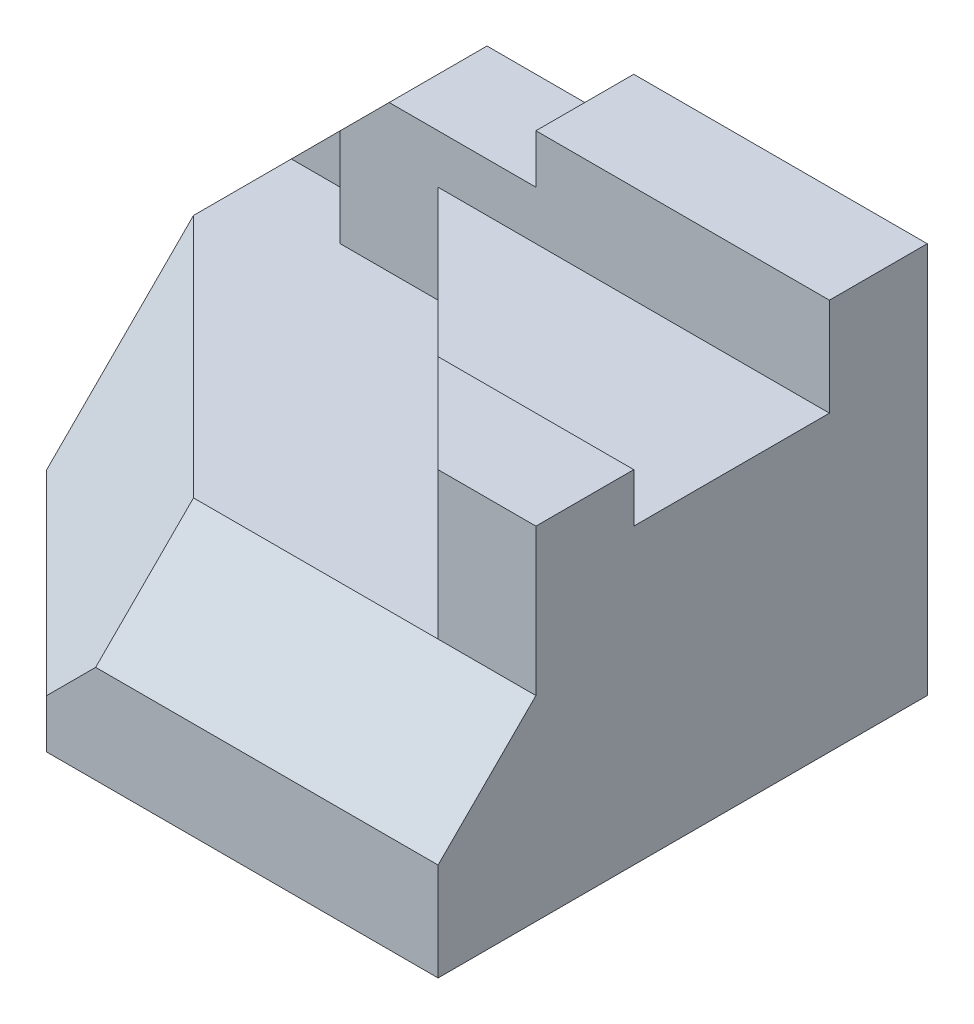
SolidWorks part; units mm, degrees
ref_plane "Front Plane" through (0, 0, 0) normal (0, 0, 1) x (1, 0, 0)
ref_plane "Top Plane" through (0, 0, 0) normal (0, 1, 0) x (1, 0, 0)
ref_plane "Right Plane" through (0, 0, 0) normal (1, 0, 0) x (0, 0, -1)
sketch "Sketch1" plane through (0, 0, 0) normal (0, 0, 1) x (1, 0, 0)
  line L1 (0, 0) -> (120, 0)
  line L2 (0, 0) -> (0, 80)
  line L3 (0, 80) -> (120, 80)
  line L4 (120, 0) -> (120, 80)
  dimension "D1" = 120
  dimension "D2" = 80
extrude "Boss-Extrude1" add sketch "Sketch1" along normal blind 100
sketch "Sketch2" plane through (0, 80, 0) normal (0, 1, 0) x (1, 0, 0)
  line L0 (0, -60) -> (40, -100)
  line L1 (0, -100) -> (0, 0) construction
  line L2 (120, -100) -> (0, -100) construction
  line L3 (40, -100) -> (0, -100)
  line L4 (0, -100) -> (0, -60)
  dimension "D1" = 40
  dimension "D2" = 40
extrude "Cut-Extrude1" cut sketch "Sketch2" against normal blind 100
sketch "Sketch3" plane through (0, 0, 0) normal (0, 0, -1) x (-1, 0, 0)
  line L0 (0, 40) -> (-30, 70)
  line L1 (0, 80) -> (0, 0) construction
  line L2 (-30, 70) -> (-60, 70)
  line L3 (-60, 70) -> (-60, 80)
  line L4 (-120, 80) -> (0, 80) construction
  line L5 (-60, 80) -> (0, 80)
  line L6 (0, 80) -> (0, 40)
  dimension "D1" = 60
  dimension "D2" = 40
  dimension "D3" = 30
  dimension "D4" = 30
extrude "Cut-Extrude2" cut sketch "Sketch3" against normal blind 100
ref_plane "Plane1" through (0, 40, 0) normal (0, 1, 0) x (1, 0, 0)
sketch "Sketch4" plane through (0, 40, 0) normal (0, 1, 0) x (1, 0, 0)
  line L0 (0, -60) -> (0, 0) construction
  line L1 (0, -20) -> (120, -20)
  line L2 (0, -20) -> (0, -100)
  line L3 (0, -100) -> (120, -100)
  line L4 (120, -20) -> (120, -100)
  dimension "D1" = 20
  dimension "D2" = 0
  dimension "D3" = 0
extrude "Cut-Extrude3" cut sketch "Sketch4" along normal blind 100
sketch "Sketch5" plane through (0, 0, 20) normal (0, 0, 1) x (1, 0, 0)
  line L0 (20, 40) -> (20, 60)
  line L1 (120, 40) -> (0, 40) construction
  line L2 (30, 70) -> (0, 40) construction
  line L3 (20, 60) -> (0, 40)
  line L4 (0, 40) -> (20, 40)
  dimension "D1" = 20
extrude "Cut-Extrude4" cut sketch "Sketch5" against normal blind 10
sketch "Sketch6" plane through (0, 40, 0) normal (0, 1, 0) x (1, 0, 0)
  line L0 (40, -20) -> (120, -20)
  line L1 (120, -20) -> (20, -20) construction
  line L2 (120, -20) -> (120, -80)
  line L3 (120, -100) -> (120, -20) construction
  line L4 (120, -80) -> (100, -80)
  line L5 (100, -80) -> (40, -20)
  dimension "D1" = 20
  dimension "D2" = 60
  dimension "D3" = 20
extrude "Boss-Extrude4" add sketch "Sketch6" along normal blind 20
sketch "Sketch8" plane through (0, 60, 0) normal (0, 1, 0) x (1, 0, 0)
  line L0 (80, -60) -> (120, -60)
  line L1 (40, -20) -> (100, -80) construction
  line L2 (120, -80) -> (120, -20) construction
  line L3 (120, -60) -> (120, -80)
  line L4 (120, -80) -> (100, -80)
  line L5 (100, -80) -> (80, -60)
  dimension "D1" = 20
extrude "Boss-Extrude5" add sketch "Sketch8" along normal blind 10
sketch "Sketch9" plane through (120, 0, 0) normal (1, 0, 0) x (0, 0, -1)
  line L0 (-100, 20) -> (-80, 40)
  line L1 (-100, 0) -> (-100, 40) construction
  line L2 (-80, 70) -> (-80, 40) construction
  line L3 (-80, 40) -> (-80, 20)
  line L4 (-80, 20) -> (-100, 20)
  line L5 (-100, 20) -> (-100, 40)
  line L6 (-100, 40) -> (-80, 40)
  dimension "D1" = 20
  dimension "D2" = 20
extrude "Cut-Extrude8" cut sketch "Sketch9" against normal blind 156 contours L6 L0 L5
sketch "Sketch10" plane through (0, 40, 0) normal (0, 1, 0) x (1, 0, 0)
  line L0 (0, -30) -> (50, -80)
  line L1 (0, -60) -> (0, -10) construction
  line L2 (20, -80) -> (100, -80) construction
  dimension "D1" = 30
  dimension "D2" = 10
sketch "Sketch12" plane through (-30, 0, 30) normal (-0.7071, 0, 0.7071) x (0.7071, 0, 0.7071)
  line L0 (42.4264, 10) -> (98.9949, 10)
  line L1 (42.4264, 0) -> (42.4264, 40) construction
  line L2 (98.9949, 20) -> (98.9949, 0) construction
  dimension "D1" = 10
ref_plane "Plane3" through (-23.3333, 23.3333, 23.3333) normal (-0.5774, 0.5774, 0.5774) x (0.8165, 0.4082, 0.4082)
sketch "Sketch13" plane through (-23.3333, 23.3333, 23.3333) normal (-0.5774, 0.5774, 0.5774) x (0.8165, 0.4082, 0.4082)
  line L0 (28.5774, 7.0711) -> (28.5774, -35.3553)
  line L1 (28.5774, -35.3553) -> (77.5672, -63.6396)
  line L2 (77.5672, -63.6396) -> (89.8146, -28.2843)
  line L3 (89.8146, -28.2843) -> (28.5774, 7.0711)
extrude "Cut-Extrude10" cut sketch "Sketch13" along normal blind 156
sketch "Sketch14" plane through (72.619, 14.5238, 58.0952) normal (-0.7715, -0.1543, -0.6172) x (-0.6052, -0.121, 0.7868)
  line L0 (53.26, 1.9612) -> (27.8405, 29.4174)
  line L1 (27.8405, 29.4174) -> (51.6713, 13.2378)
  line L2 (51.6713, 13.2378) -> (53.26, 1.9612)
extrude "Cut-Extrude11" cut sketch "Sketch14" against normal blind 156
sketch "Sketch15" plane through (-33.2215, 0.8979, 41.3024) normal (0.6267, -0.0169, -0.7791) x (-0.7793, -0.0136, -0.6265)
  line L0 (-94.3065, 17.8219) -> (-92.3557, 19.0987)
  line L1 (-92.3557, 19.0987) -> (-93.9597, 7.8242)
  line L2 (-93.9597, 7.8242) -> (-94.3065, 17.8219)
  line L3 (-93.9597, 7.8242) -> (-94.3065, 17.8219) construction
extrude "Cut-Extrude12" cut sketch "Sketch15" against normal blind 156
